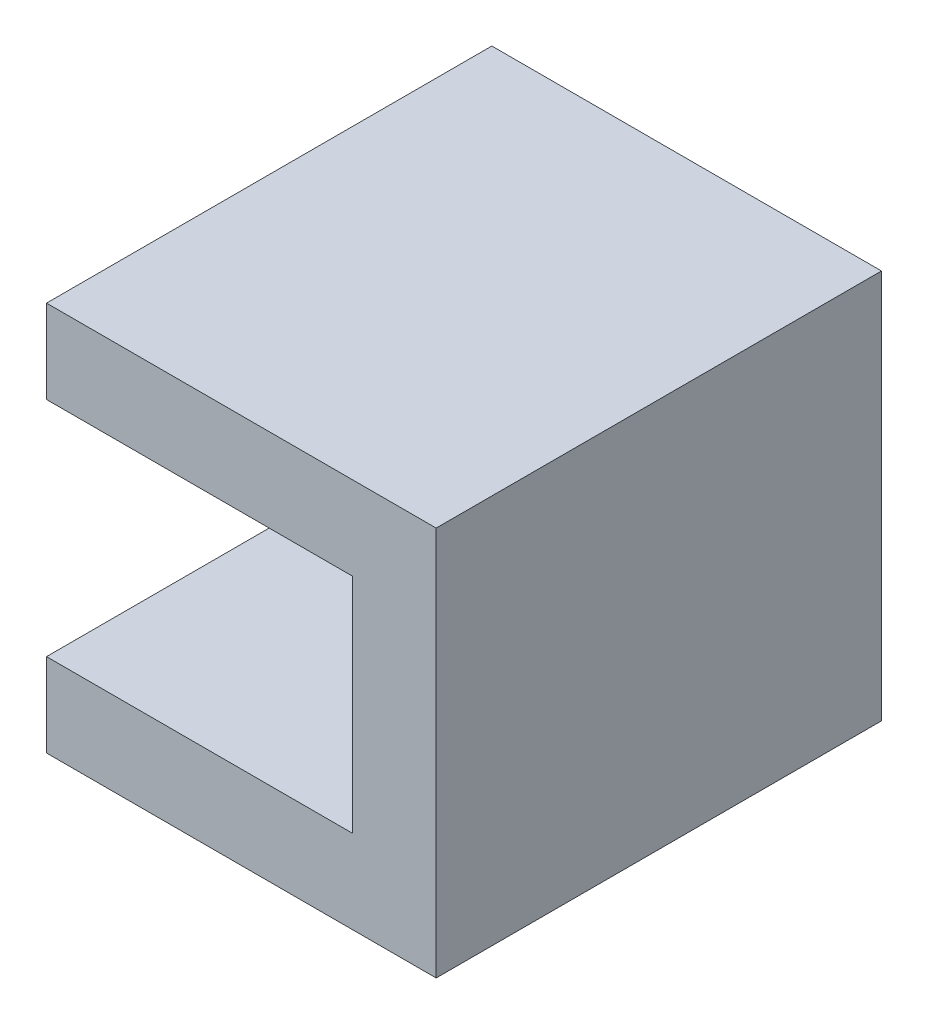
SolidWorks part; units mm, degrees
ref_plane "Front Plane" through (0, 0, 0) normal (0, 0, 1) x (1, 0, 0)
ref_plane "Top Plane" through (0, 0, 0) normal (0, 1, 0) x (1, 0, 0)
ref_plane "Right Plane" through (0, 0, 0) normal (1, 0, 0) x (0, 0, -1)
sketch "Sketch1" plane through (0, 0, 0) normal (0, 0, 1) x (1, 0, 0)
  line L0 (-31.75, 22.225) -> (-31.75, 12.7)
  line L1 (-31.75, 12.7) -> (-17.4625, 12.7)
  line L2 (3.175, 12.7) -> (3.175, 0)
  line L3 (3.175, -12.7) -> (-11.1125, -12.7)
  line L4 (-31.75, -12.7) -> (-31.75, -22.225)
  line L5 (-31.75, -22.225) -> (12.7, -22.225)
  line L6 (12.7, -22.225) -> (12.7, 22.225)
  line L7 (12.7, 22.225) -> (-31.75, 22.225)
  line L8 (3.175, 12.7) -> (12.7, 12.7) construction
  line L9 (3.175, 0) -> (0, 0)
  line L10 (0, 0) -> (0, -6.35)
  line L11 (0, -6.35) -> (3.175, -6.35)
  line L14 (-17.4625, 12.7) -> (-17.4625, 9.525)
  line L15 (-17.4625, 9.525) -> (-11.1125, 9.525)
  line L16 (-11.1125, 9.525) -> (-11.1125, 12.7)
  line L17 (55, 0) -> (-55, 0) construction
  line L18 (-17.4625, -12.7) -> (-17.4625, -9.525)
  line L19 (-17.4625, -9.525) -> (-11.1125, -9.525)
  line L20 (-11.1125, -9.525) -> (-11.1125, -12.7)
  line L21 (-17.4625, 12.7) -> (-11.1125, 12.7) construction
  line L22 (-11.1125, 12.7) -> (3.175, 12.7)
  line L23 (3.175, 0) -> (3.175, -6.35) construction
  line L24 (3.175, -6.35) -> (3.175, -12.7)
  line L25 (-11.1125, -12.7) -> (-17.4625, -12.7) construction
  line L26 (-17.4625, -12.7) -> (-31.75, -12.7)
  point P8 (12.7, 0)
  dimension "D1" = 44.45
  dimension "D2" = 9.525
  dimension "D3" = 3.175
  dimension "D4" = 6.35
extrude "Boss-Extrude1" add sketch "Sketch1" along normal mid plane 50.8
sketch "Sketch2" plane through (-17.4625, 0, 0) normal (-1, 0, 0) x (0, 0, 1)
  line L0 (-25.4, -9.525) -> (-25.4, -12.7) construction
  line L1 (-25.4, -12.7) -> (25.4, -12.7) construction
  line L2 (25.4, -12.7) -> (25.4, -9.525) construction
  line L3 (25.4, -9.525) -> (-25.4, -9.525) construction
  line L4 (-25.4, 12.7) -> (-25.4, 9.525) construction
  line L5 (-25.4, 9.525) -> (25.4, 9.525) construction
  line L6 (25.4, 9.525) -> (25.4, 12.7) construction
  line L7 (25.4, 12.7) -> (-25.4, 12.7) construction
  line L8 (-25.4, -9.525) -> (-25.4, -12.7)
  line L9 (-25.4, -12.7) -> (-3.175, -12.7)
  line L10 (25.4, -12.7) -> (25.4, -9.525)
  line L11 (25.4, -9.525) -> (-25.4, -9.525)
  line L12 (-25.4, 12.7) -> (-25.4, 9.525)
  line L13 (-25.4, 9.525) -> (25.4, 9.525)
  line L14 (25.4, 9.525) -> (25.4, 12.7)
  line L15 (25.4, 12.7) -> (3.175, 12.7)
  line L16 (-3.175, -12.7) -> (3.175, -12.7) construction
  line L17 (3.175, -12.7) -> (25.4, -12.7)
  line L18 (25.4, -12.7) -> (-25.4, -12.7) construction
  line L19 (3.175, 12.7) -> (-3.175, 12.7) construction
  line L20 (-3.175, 12.7) -> (-25.4, 12.7)
  arc A0 (-3.175, 12.7) -> (3.175, 12.7) centre (0, 12.7) ccw
  arc A1 (3.175, -12.7) -> (-3.175, -12.7) centre (0, -12.7) ccw
  arc A2 (-3.175, -12.7) -> (3.175, -12.7) centre (0, -12.7) ccw construction
  arc A3 (3.175, 12.7) -> (-3.175, 12.7) centre (0, 12.7) ccw construction
  point P17 (0, -9.525)
  point P23 (0, 9.525)
  line M7 (-25.4, 12.7) -> (-25.4, 9.525)
  line M8 (-25.4, 9.525) -> (25.4, 9.525)
  line M9 (25.4, 9.525) -> (25.4, 12.7)
  line M10 (25.4, 12.7) -> (-25.4, 12.7)
extrude "Cut-Extrude1" cut sketch "Sketch2" against normal up to surface (6.35 mm away) contours A0 L13 M9 M10 | A0 M10 M7 M8 | A1 L11 L8 L9 | A1 L17 L10 L11 up to face at (-11.1125, -11.1125, 0)
sketch "Sketch3" plane through (0, 0, 0) normal (0, 1, 0) x (1, 0, 0)
  line L0 (3.175, -3.175) -> (3.175, 3.175) construction
  line L1 (3.175, 3.175) -> (3.175, 25.4) construction
  line L2 (0, 25.4) -> (0, 0) construction
  line L4 (3.175, 25.4) -> (0, 25.4)
  line L5 (0, 25.4) -> (0, -25.4)
  line L6 (0, -25.4) -> (3.175, -25.4)
  line L7 (3.175, -25.4) -> (3.175, 25.4)
  line L8 (3.175, 25.4) -> (0, 25.4) construction
  line L9 (0, 0) -> (0, -25.4)
  line L10 (0, -25.4) -> (3.175, -25.4)
  line L11 (3.175, -25.4) -> (3.175, -3.175)
  arc A0 (0, 0) -> (3.175, -3.175) centre (3.175, 0) ccw
  arc A1 (3.175, -3.175) -> (3.175, 3.175) centre (3.175, 0) ccw construction
  arc A2 (3.175, 3.175) -> (0, 0) centre (3.175, 0) ccw construction
  dimension "D1" = 0
extrude "Cut-Extrude2" cut sketch "Sketch3" against normal up to surface (6.35 mm away) up to face at (1.5875, -6.35, 0)
mirror "Mirror1" about plane through (0, 0, 0) normal (0, 0, 1) of "Cut-Extrude2"
